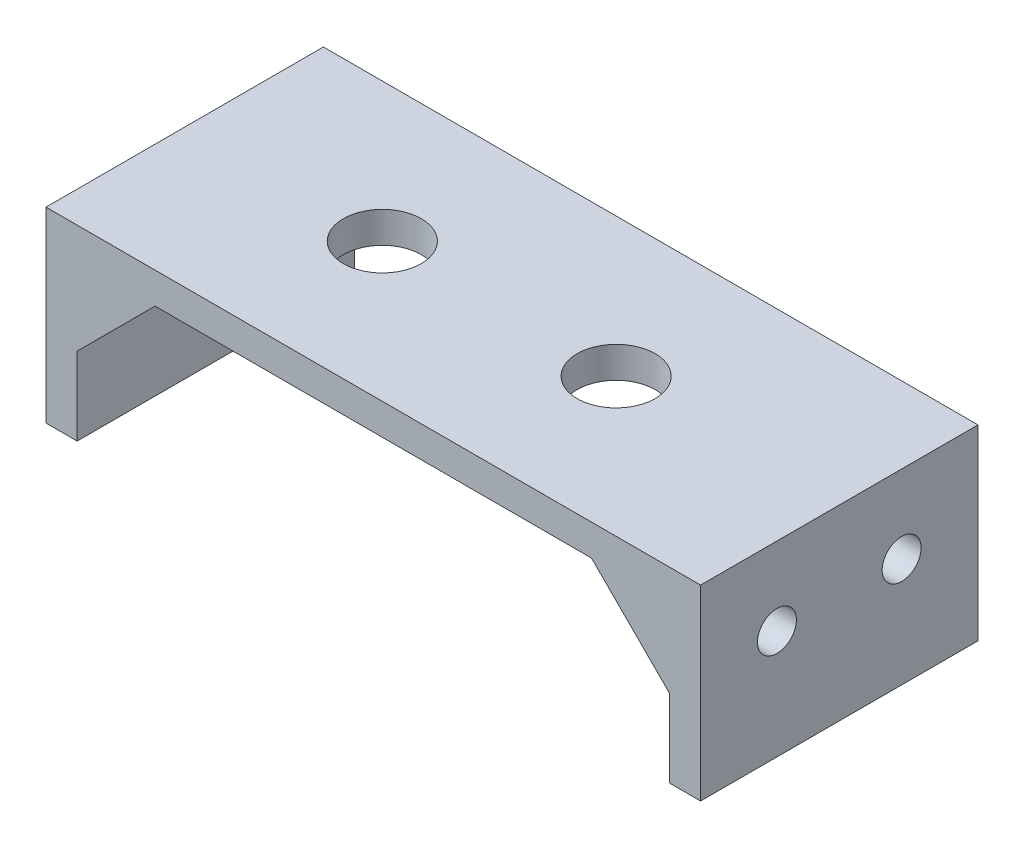
SolidWorks part; units mm, degrees
ref_plane "Front Plane" through (0, 0, 0) normal (0, 0, 1) x (1, 0, 0)
ref_plane "Top Plane" through (0, 0, 0) normal (0, 1, 0) x (1, 0, 0)
ref_plane "Right Plane" through (0, 0, 0) normal (1, 0, 0) x (0, 0, -1)
sketch "Sketch2" plane through (0, 0, 0) normal (0, 1, 0) x (1, 0, 0)
  line L1 (-21, 8.9) -> (21, 8.9)
  line L2 (-21, 8.9) -> (-21, -8.9)
  line L3 (-21, -8.9) -> (21, -8.9)
  line L4 (21, 8.9) -> (21, -8.9)
  line L5 (-21, 8.9) -> (21, -8.9) construction
  line L6 (-21, -8.9) -> (21, 8.9) construction
  point P0 (0, 0)
  dimension "D1" = 17.8
  dimension "D2" = 42
extrude "Boss-Extrude1" add sketch "Sketch2" along normal blind 2
sketch "Sketch3" plane through (0, 0, 0) normal (0, -1, 0) x (1, 0, 0)
  line L0 (21, -8.9) -> (-21, -8.9) construction
  line L1 (-21, 8.9) -> (-19, 8.9)
  line L2 (-21, 8.9) -> (-21, -8.9)
  line L3 (-21, -8.9) -> (-19, -8.9)
  line L4 (-19, 8.9) -> (-19, -8.9)
  line L5 (-21, 8.9) -> (21, 8.9) construction
  line L6 (21, 8.9) -> (19, 8.9)
  line L7 (21, 8.9) -> (21, -8.9)
  line L8 (21, -8.9) -> (19, -8.9)
  line L9 (19, 8.9) -> (19, -8.9)
  line L10 (21, 8.9) -> (21, -8.9) construction
  dimension "D1" = 2
  dimension "D2" = 2
extrude "Boss-Extrude2" add sketch "Sketch3" along normal blind 10
sketch "Sketch4" plane through (0, 0, 8.9) normal (0, 0, 1) x (1, 0, 0)
  line L0 (-19, 0) -> (19, 0) construction
  line L1 (-19, 0) -> (-14, 0)
  line L2 (-19, -10) -> (-19, 0) construction
  line L3 (-19, -5) -> (-19, 0)
  line L4 (-19, -5) -> (-14, 0)
  line L5 (0, 2) -> (0, 0) construction
  line L6 (-21, 2) -> (21, 2) construction
  line L7 (19, -5) -> (14, 0)
  line L8 (19, 0) -> (14, 0)
  line L9 (19, -5) -> (19, 0)
  dimension "D1" = 5
  dimension "D2" = 5
extrude "Boss-Extrude3" add sketch "Sketch4" against normal blind 2
mirror "Mirror1" about plane through (0, 0, 0) normal (0, 0, 1) of "Boss-Extrude3"
sketch "Sketch5" plane through (0, 0, 0) normal (0, -1, 0) x (1, 0, 0)
  line L0 (-19, 0) -> (19, 0) construction
  line L1 (-19, -8.9) -> (-19, 8.9) construction
  line L2 (19, 8.9) -> (19, -8.9) construction
  circle A0 centre (-8.3199, 0) radius 2.5
  circle A1 centre (6.6801, 0) radius 2.5
  dimension "D1" = 5
  dimension "D2" = 5
  dimension "D3" = 15
extrude "Cut-Extrude1" cut sketch "Sketch5" against normal blind 2
sketch "Sketch6" plane through (-19, 0, 0) normal (1, 0, 0) x (0, 0, -1)
  line L0 (8.9, -10) -> (-8.9, -10) construction
  line L1 (0, 0) -> (0, -10) construction
  line L2 (6.9, 0) -> (-6.9, 0) construction
  circle A0 centre (-4, -3) radius 1.25
  circle A1 centre (4, -3) radius 1.25
  dimension "D1" = 2.5
  dimension "D2" = 2.5
  dimension "D3" = 8
  dimension "D4" = 3
  dimension "D5" = 3
  dimension "D6" = 4
extrude "Cut-Extrude2" cut sketch "Sketch6" against normal blind 2
mirror "Mirror2" about plane through (0, 0, 0) normal (1, 0, 0) of "Cut-Extrude2"
